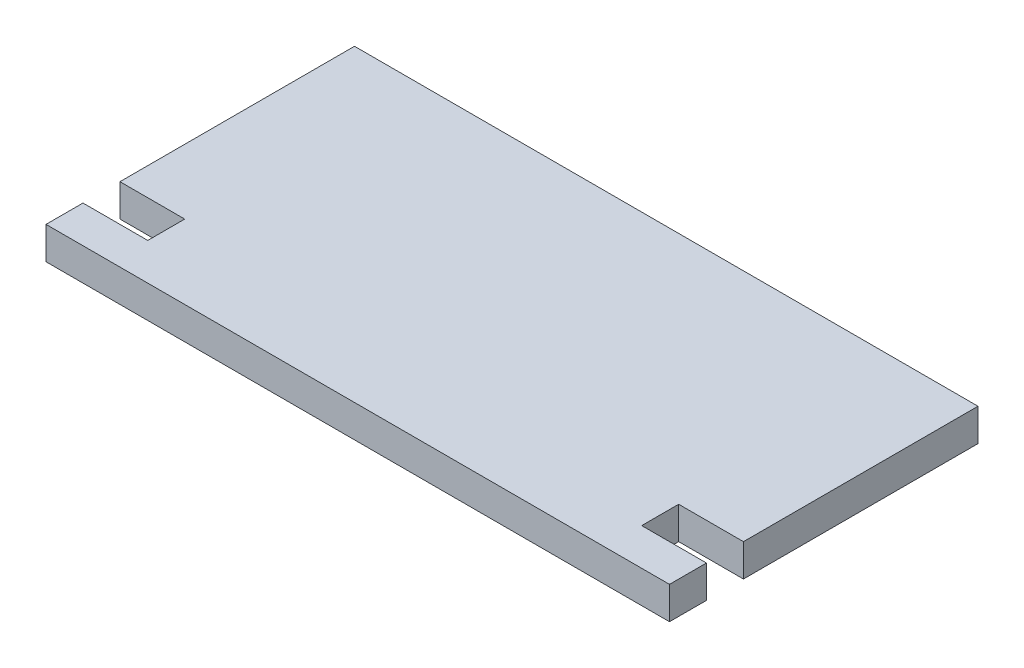
SolidWorks part; units mm, degrees
ref_plane "Front Plane" through (0, 0, 0) normal (0, 0, 1) x (1, 0, 0)
ref_plane "Top Plane" through (0, 0, 0) normal (0, 1, 0) x (1, 0, 0)
ref_plane "Right Plane" through (0, 0, 0) normal (1, 0, 0) x (0, 0, -1)
sketch "Sketch1" plane through (0, 0, 0) normal (0, 1, 0) x (1, 0, 0)
  line L0 (0, 5.715) -> (0, -5.715) construction
  line L1 (-11.55, 5.715) -> (11.55, 5.715)
  line L2 (-11.55, 5.715) -> (-11.55, -5.715)
  line L3 (-11.55, -5.715) -> (11.55, -5.715)
  line L4 (11.55, 5.715) -> (11.55, -5.715)
  line L5 (-11.55, 5.715) -> (11.55, -5.715) construction
  line L6 (-11.55, -5.715) -> (11.55, 5.715) construction
  line L7 (9.15, -2.975) -> (11.55, -2.975)
  line L8 (-9.15, -4.345) -> (-11.55, -4.345)
  line L9 (-9.15, -4.345) -> (-9.15, -2.975)
  line L10 (-9.15, -2.975) -> (-11.55, -2.975)
  line L11 (-11.55, -4.345) -> (-11.55, -2.975)
  line L12 (-9.15, -4.345) -> (-11.55, -2.975) construction
  line L13 (-9.15, -2.975) -> (-11.55, -4.345) construction
  line L14 (11.55, -4.345) -> (11.55, -2.975)
  line L15 (9.15, -4.345) -> (11.55, -4.345)
  line L16 (9.15, -4.345) -> (9.15, -2.975)
  point P0 (0, 0)
  point P8 (-10.35, -3.66)
  dimension "D1" = 23.1
  dimension "D2" = 11.43
  dimension "D3" = 2.4
  dimension "D4" = 1.37
  dimension "0.7" = 1.37
extrude "Boss-Extrude1" add sketch "Sketch1" along normal blind 1.2 contours L15 L16 L7 L4 L1 L2 L10 L9 L8 L3
